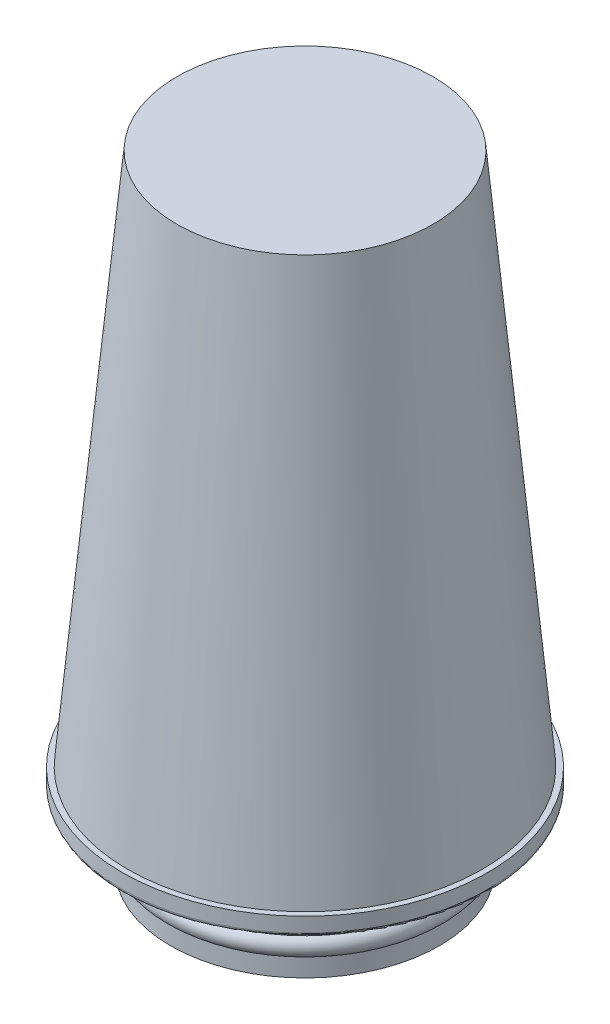
SolidWorks part; units mm, degrees
ref_plane "Front Plane" through (0, 0, 0) normal (0, 0, 1) x (1, 0, 0)
ref_plane "Top Plane" through (0, 0, 0) normal (0, 1, 0) x (1, 0, 0)
ref_plane "Right Plane" through (0, 0, 0) normal (1, 0, 0) x (0, 0, -1)
sketch "Sketch1" plane through (0, 0, 0) normal (0, 0, 1) x (1, 0, 0)
  line L0 (36.75, 10) -> (36.75, 18)
  line L1 (36.75, 0) -> (36.75, 5)
  line L2 (37.75, 19) -> (49, 19)
  line L3 (35.25, 0) -> (35.25, 6.1771)
  line L4 (50, 20) -> (50, 24)
  line L5 (35.25, 8.8229) -> (35.25, 18)
  line L6 (0, 170) -> (0, 159)
  line L7 (0, 170) -> (0, 159)
  line L8 (48.5, 24) -> (50, 24)
  line L9 (35.25, 0) -> (36.75, 0)
  line L10 (0, 170) -> (35, 170)
  line L11 (35, 170) -> (48.5, 24)
  line L12 (0, 170) -> (0, 0) construction
  line L13 (37.75, 20.5) -> (24.9435, 159)
  line L14 (24.9435, 159) -> (0, 159)
  line L16 (37.75, 20.5) -> (48.5, 20.5) construction
  line L17 (48.5, 20.5) -> (48.5, 24) construction
  arc A0 (36.75, 5) -> (36.75, 10) centre (35.4167, 7.5) ccw
  arc A1 (36.75, 18) -> (37.75, 19) centre (37.75, 18) cw
  arc A2 (49, 19) -> (50, 20) centre (49, 20) ccw
  arc A3 (35.25, 6.1771) -> (35.25, 8.8229) centre (35.4167, 7.5) ccw
  arc A4 (35.25, 18) -> (37.75, 20.5) centre (37.75, 18) cw
  arc A6 (48.5, 20.5) -> (48.5, 20.5) centre (48.5, 20.5) ccw construction
  point P3 (38.25, 7.5)
  point P12 (36.75, 19)
  dimension "D7" = 1
  dimension "D1" = 36.75
  dimension "D2" = 5
  dimension "D3" = 5
  dimension "D4" = 38.25
  dimension "D5" = 19
  dimension "D6" = 50
  dimension "D9" = 5
  dimension "D10" = 35
  dimension "D11" = 170
  dimension "D12" = 11
  dimension "D8" = 1.5
revolve "Revolve1" add sketch "Sketch1" angle 360 about L12
